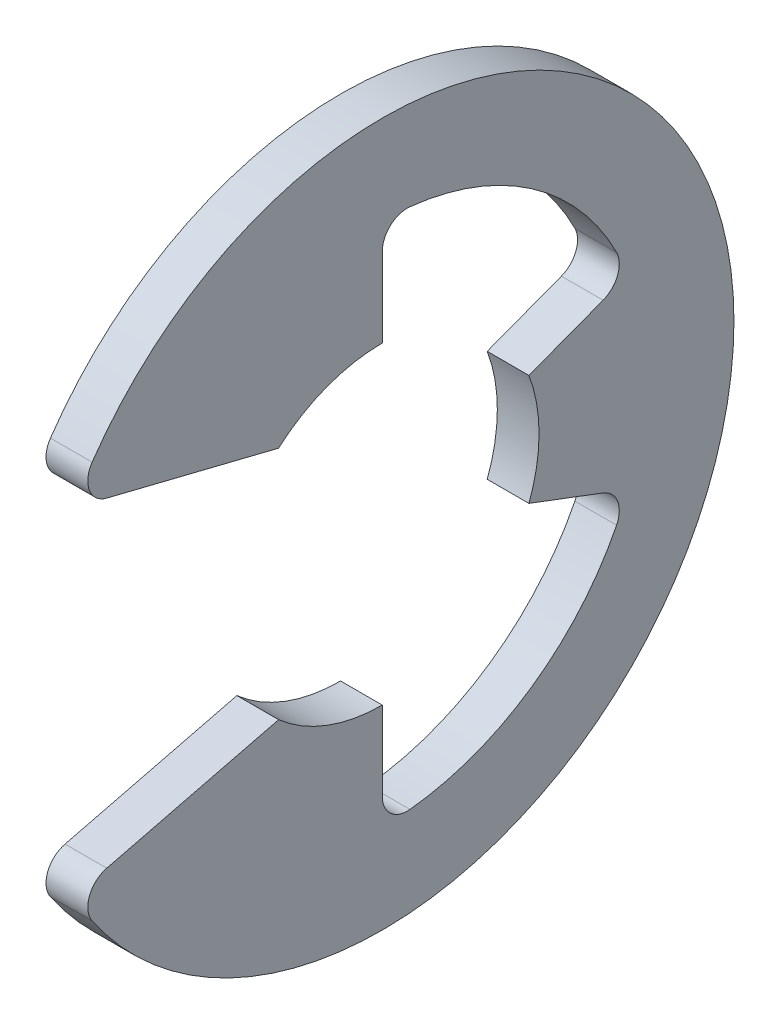
SolidWorks part; units mm, degrees
ref_plane "Front" through (0, 0, 0) normal (0, 0, 1) x (1, 0, 0)
ref_plane "Top" through (0, 0, 0) normal (0, 1, 0) x (1, 0, 0)
ref_plane "Right" through (0, 0, 0) normal (1, 0, 0) x (0, 0, -1)
sketch "Sketch1" plane through (0, 0, 0) normal (1, 0, 0) x (0, 0, -1)
  line L0 (-5.179, -2.8264) -> (-1.7396, -1.9725)
  line L1 (-5.179, 2.8264) -> (-1.7396, 1.9725)
  line L2 (0, -2.63) -> (0, -4.4026)
  line L3 (0, 2.63) -> (0, 4.4026)
  line L4 (2.4601, -0.9298) -> (4.1182, -1.5565)
  line L5 (2.4601, 0.9298) -> (4.1182, 1.5565)
  line L6 (0, 0) -> (-6.15, 0) construction
  line L7 (2.4601, 0.9298) -> (2.4601, -0.9298) construction
  line L8 (0, -2.63) -> (-1.7396, -1.9725) construction
  circle A1 centre (0, 0) radius 6.15 construction
  circle A2 centre (0, 0) radius 2.63 construction
  arc A3 (-5.179, -2.8264) -> (-5.179, 2.8264) centre (0, 0) ccw
  arc A4 (-1.7396, -1.9725) -> (0, -2.63) centre (0, 0) ccw
  arc A5 (-1.7396, 1.9725) -> (0, 2.63) centre (0, 0) cw
  arc A6 (2.4601, 0.9298) -> (2.4601, -0.9298) centre (0, 0) cw
  arc A7 (0, -4.4026) -> (4.1182, -1.5565) centre (0, 0) ccw
  arc A8 (4.1182, 1.5565) -> (0, 4.4026) centre (0, 0) ccw
  dimension "D1" = 4.4026
  dimension "OD" = 11.8
  dimension "L" = 12.3
  dimension "D" = 5.26
  dimension "D2" = 2.9905
  dimension "D3" = 3.945
extrude "Extrude1" add sketch "Sketch1" along normal mid plane 0.7
fillet "Fillet1" radius 0.42 6 edges at (0, -4.4026, 0) (0, 4.4026, 0) (0, -2.8264, 5.179) (0, 2.8264, 5.179) (0, -1.5565, -4.1182) (0, 1.5565, -4.1182)
sketch "Sketch3" plane through (0, 0, 0) normal (0, 1, 0) x (1, 0, 0)
  line L0 (0.37, 3.5) -> (0.37, 3)
  line L1 (0.37, 3) -> (-0.37, 3)
  line L2 (-0.37, 3) -> (-0.37, 3.5)
  line L3 (-0.37, 3.5) -> (-5.18, 3.5)
  line L4 (2.22, 0) -> (2.22, 3.25)
  line L5 (-5.18, 3.5) -> (-5.18, 0)
  line L6 (-5.18, 0) -> (2.22, 0)
  line L8 (2.22, 0) -> (2.22, 3.5) construction
  line L9 (2.22, 3.5) -> (0.37, 3.5) construction
  line L10 (2.22, 0) -> (17.2631, 0) construction
  line L11 (2.22, 3.25) -> (1.97, 3.5)
  line L12 (1.97, 3.5) -> (0.37, 3.5)
  point P2 (0, 3)
  point P5 (0.37, 3.25)
  dimension "D1" = 1.85
  dimension "Ds" = 7
  dimension "Dg" = 6
  dimension "W" = 0.74
  dimension "D2" = 7.4
  dimension "D3" = 45
revolve "Revolve2" [suppressed] add sketch "Sketch3" angle 360 about L10
equation "\"D2@Sketch3\" = \"W@Sketch3\"*10"
equation "\"D1@Sketch3\" = \"D2@Sketch3\"/4"
equation "\"D1@Sketch1\" = (\"OD@Sketch1\"+\"D@Sketch1\")/3.875"
equation "\"D3@Sketch1\" = \"D@Sketch1\"*.75"
equation "\"D1@Fillet1\" = \"D1@Extrude1\"*.6"
